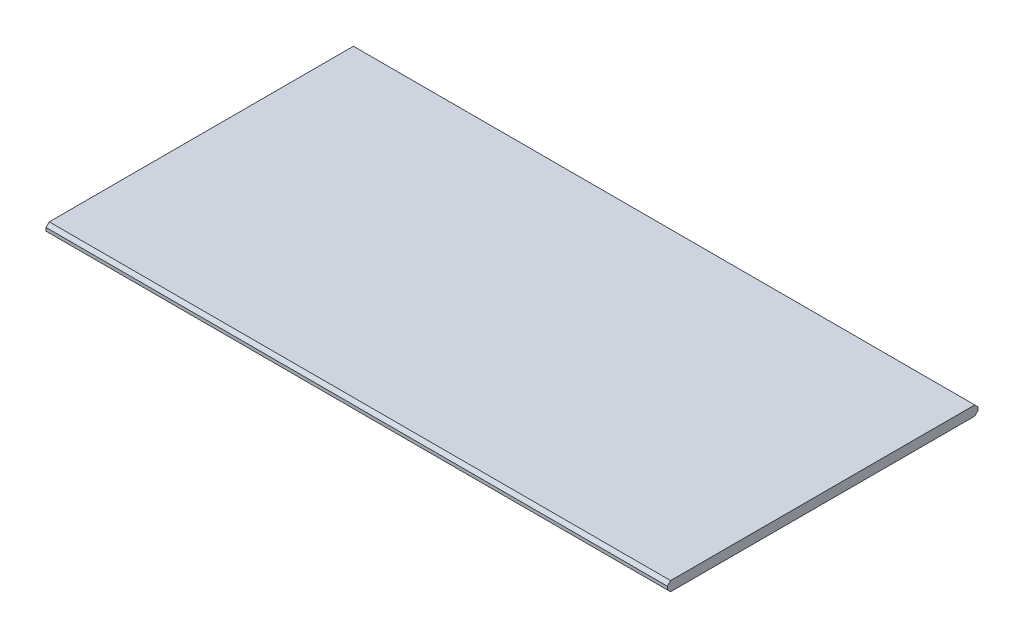
SolidWorks part; units mm, degrees
material "Pine"
ref_plane "Front Plane" through (0, 0, 0) normal (0, 0, 1) x (1, 0, 0)
ref_plane "Top Plane" through (0, 0, 0) normal (0, 1, 0) x (1, 0, 0)
ref_plane "Right Plane" through (0, 0, 0) normal (1, 0, 0) x (0, 0, -1)
sketch "Sketch1" plane through (0, 0, 0) normal (0, 1, 0) x (1, 0, 0)
  line L1 (-609.6, 304.8) -> (609.6, 304.8)
  line L2 (-609.6, 304.8) -> (-609.6, -304.8)
  line L3 (-609.6, -304.8) -> (609.6, -304.8)
  line L4 (609.6, 304.8) -> (609.6, -304.8)
  line L5 (-609.6, 304.8) -> (609.6, -304.8) construction
  line L6 (-609.6, -304.8) -> (609.6, 304.8) construction
  point P0 (0, 0)
  dimension "D1" = 1219.2
  dimension "D2" = 609.6
extrude "Boss-Extrude1" add sketch "Sketch1" along normal mid plane 19.05
chamfer "Chamfer1" distance 6.35 angle 45 4 edges at (0, -9.525, -304.8) (0, 9.525, -304.8) (0, -9.525, 304.8) (0, 9.525, 304.8)
